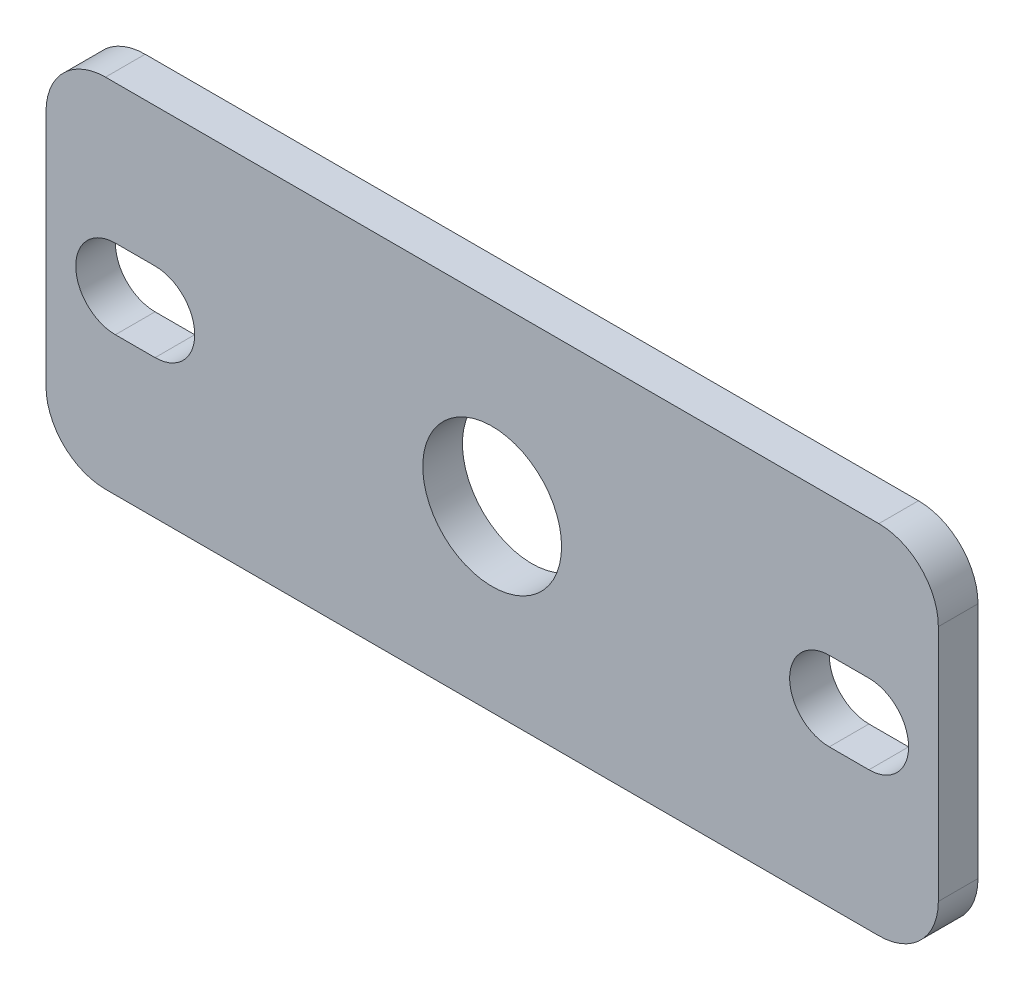
SolidWorks part; units mm, degrees
material "PVC 0.007 plastifié"
ref_plane "Face" through (0, 0, 0) normal (0, 0, 1) x (1, 0, 0)
ref_plane "Dessus" through (0, 0, 0) normal (0, 1, 0) x (1, 0, 0)
ref_plane "Droite" through (0, 0, 0) normal (1, 0, 0) x (0, 0, -1)
sketch "Esquisse1" plane through (0, 0, 0) normal (0, 0, 1) x (1, 0, 0)
  line L0 (0, 0) -> (0, 46.5943) construction
  line L1 (-22.5, 9) -> (22.5, 9)
  line L2 (-22.5, 9) -> (-22.5, -9)
  line L4 (22.5, 9) -> (22.5, -9)
  line L5 (0, 0) -> (57.4796, 0) construction
  line L9 (-22.5, -9) -> (22.5, -9)
  dimension "D1" = 45
  dimension "D2" = 18
extrude "Extrusion1" add sketch "Esquisse1" along normal blind 2
fillet "Congé1" radius 3 4 edges at (22.5, 9, 1) (-22.5, 9, 1) (22.5, -9, 1) (-22.5, -9, 1)
sketch "Esquisse2" plane through (0, 0, 2) normal (0, 0, 1) x (1, 0, 0)
  line L1 (0, 0) -> (25.4902, 0) construction
  line L2 (0, 0) -> (0, 21.0064) construction
  line L3 (25.4902, 0) -> (0, 0) construction
  line L4 (0, 0) -> (0, 22.1388) construction
  line L5 (17, 2) -> (19, 2)
  line L6 (19, -2) -> (17, -2)
  line L7 (-19, -2) -> (-17, -2)
  line L8 (-17, 2) -> (-19, 2)
  arc A0 (19, -2) -> (19, 2) centre (19, 0) ccw
  arc A1 (17, -2) -> (17, 2) centre (17, 0) cw
  circle A2 centre (0, 0) radius 3.5
  arc A3 (-17, -2) -> (-17, 2) centre (-17, 0) ccw
  arc A4 (-19, -2) -> (-19, 2) centre (-19, 0) cw
  dimension "D1" = 4
  dimension "D4" = 7
  dimension "D2" = 4
  dimension "D3" = 2
  dimension "D5" = 17
extrude "Enlèv. mat.-Extru.1" cut sketch "Esquisse2" against normal up to next
